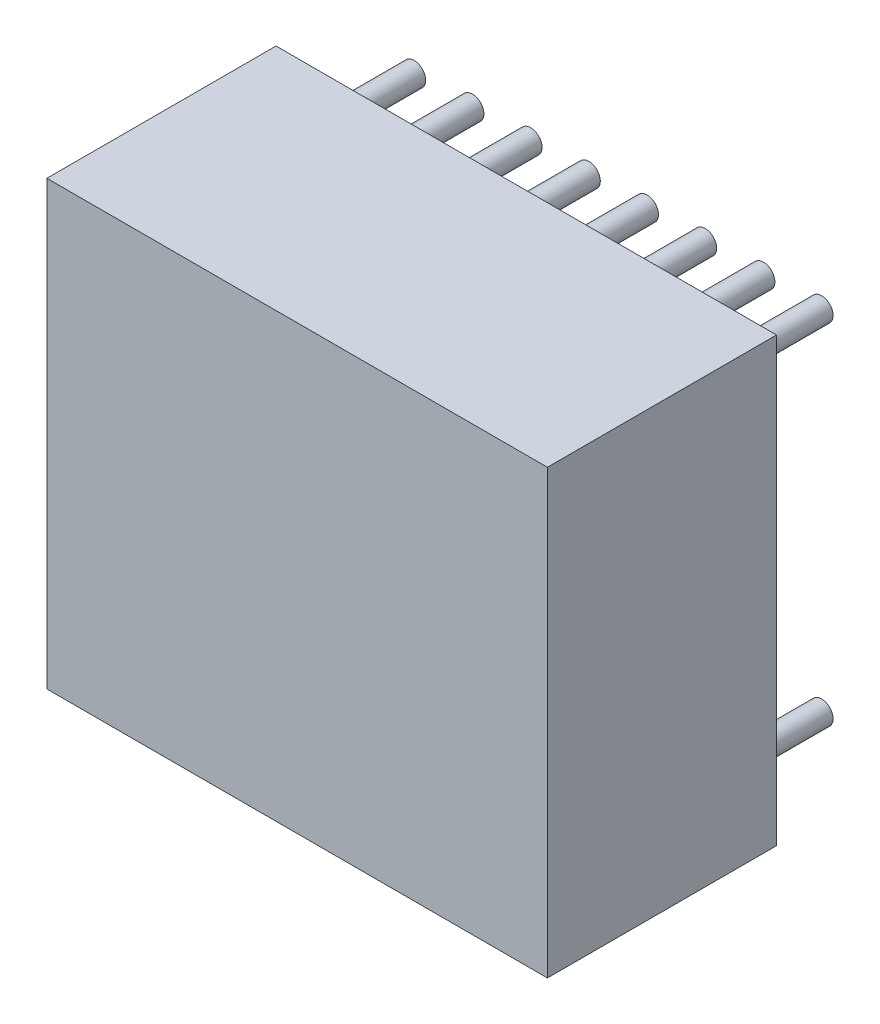
SolidWorks part; units mm, degrees
ref_plane "Front Plane" through (0, 0, 0) normal (0, 0, 1) x (1, 0, 0)
ref_plane "Top Plane" through (0, 0, 0) normal (0, 1, 0) x (1, 0, 0)
ref_plane "Right Plane" through (0, 0, 0) normal (1, 0, 0) x (0, 0, -1)
sketch "Sketch1" plane through (0, 0, 0) normal (0, 0, 1) x (1, 0, 0)
  line L0 (-1.016, 8.636) -> (-1.016, -1.016)
  line L1 (-1.016, -1.016) -> (9.906, -1.016)
  line L2 (9.906, -1.016) -> (9.906, 8.636)
  line L3 (9.906, 8.636) -> (-1.016, 8.636)
extrude "Component_Outline" add sketch "Sketch1" along normal blind 5 separate body
sketch "Sketch2" plane through (0, 0, 0) normal (0, 0, 1) x (1, 0, 0)
  circle A0 centre (0, 0) radius 0.25
extrude "1" add sketch "Sketch2" against normal blind 2 separate body
sketch "Sketch3" plane through (0, 0, 0) normal (0, 0, 1) x (1, 0, 0)
  circle A0 centre (1.27, 0) radius 0.25
extrude "2" add sketch "Sketch3" against normal blind 2 separate body
sketch "Sketch4" plane through (0, 0, 0) normal (0, 0, 1) x (1, 0, 0)
  circle A0 centre (2.54, 0) radius 0.25
extrude "3" add sketch "Sketch4" against normal blind 2 separate body
sketch "Sketch5" plane through (0, 0, 0) normal (0, 0, 1) x (1, 0, 0)
  circle A0 centre (3.81, 0) radius 0.25
extrude "4" add sketch "Sketch5" against normal blind 2 separate body
sketch "Sketch6" plane through (0, 0, 0) normal (0, 0, 1) x (1, 0, 0)
  circle A0 centre (5.08, 0) radius 0.25
extrude "5" add sketch "Sketch6" against normal blind 2 separate body
sketch "Sketch7" plane through (0, 0, 0) normal (0, 0, 1) x (1, 0, 0)
  circle A0 centre (6.35, 0) radius 0.25
extrude "6" add sketch "Sketch7" against normal blind 2 separate body
sketch "Sketch8" plane through (0, 0, 0) normal (0, 0, 1) x (1, 0, 0)
  circle A0 centre (7.62, 0) radius 0.25
extrude "7" add sketch "Sketch8" against normal blind 2 separate body
sketch "Sketch9" plane through (0, 0, 0) normal (0, 0, 1) x (1, 0, 0)
  circle A0 centre (8.89, 0) radius 0.25
extrude "8" add sketch "Sketch9" against normal blind 2 separate body
sketch "Sketch10" plane through (0, 0, 0) normal (0, 0, 1) x (1, 0, 0)
  circle A0 centre (8.89, 7.62) radius 0.25
extrude "9" add sketch "Sketch10" against normal blind 2 separate body
sketch "Sketch11" plane through (0, 0, 0) normal (0, 0, 1) x (1, 0, 0)
  circle A0 centre (7.62, 7.62) radius 0.25
extrude "10" add sketch "Sketch11" against normal blind 2 separate body
sketch "Sketch12" plane through (0, 0, 0) normal (0, 0, 1) x (1, 0, 0)
  circle A0 centre (6.35, 7.62) radius 0.25
extrude "11" add sketch "Sketch12" against normal blind 2 separate body
sketch "Sketch13" plane through (0, 0, 0) normal (0, 0, 1) x (1, 0, 0)
  circle A0 centre (5.08, 7.62) radius 0.25
extrude "12" add sketch "Sketch13" against normal blind 2 separate body
sketch "Sketch14" plane through (0, 0, 0) normal (0, 0, 1) x (1, 0, 0)
  circle A0 centre (3.81, 7.62) radius 0.25
extrude "13" add sketch "Sketch14" against normal blind 2 separate body
sketch "Sketch15" plane through (0, 0, 0) normal (0, 0, 1) x (1, 0, 0)
  circle A0 centre (2.54, 7.62) radius 0.25
extrude "14" add sketch "Sketch15" against normal blind 2 separate body
sketch "Sketch16" plane through (0, 0, 0) normal (0, 0, 1) x (1, 0, 0)
  circle A0 centre (1.27, 7.62) radius 0.25
extrude "15" add sketch "Sketch16" against normal blind 2 separate body
sketch "Sketch17" plane through (0, 0, 0) normal (0, 0, 1) x (1, 0, 0)
  circle A0 centre (0, 7.62) radius 0.25
extrude "16" add sketch "Sketch17" against normal blind 2 separate body
sketch3d "3DSketch1"
  line L0 (0, 0, 0) -> (1, 0, 0)
  line L1 (0, 0, 0) -> (0, 1, 0)
  line L2 (0, 0, 0) -> (0, 0, 1)
  point P0 (0, 0, 0)
